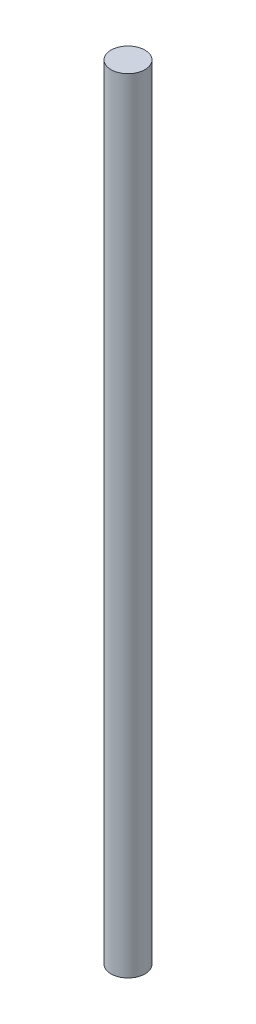
SolidWorks part; units mm, degrees
material "Chromium Copper, UNS C18200"
ref_plane "Front Plane" through (0, 0, 0) normal (0, 0, 1) x (1, 0, 0)
ref_plane "Top Plane" through (0, 0, 0) normal (0, 1, 0) x (1, 0, 0)
ref_plane "Right Plane" through (0, 0, 0) normal (1, 0, 0) x (0, 0, -1)
sketch "Sketch1" plane through (0, 0, 0) normal (0, 1, 0) x (1, 0, 0)
  circle A0 centre (0, 0) radius 1.8415
  dimension "D1" = 3.683
extrude "Boss-Extrude1" add sketch "Sketch1" along normal blind 84.963
cosmetic thread "Cosmetic Thread1" parameters "D1"=4.445, "D2"=2.5603
cosmetic thread "Cosmetic Thread2" parameters "D1"=4.445, "D2"=2.5603
